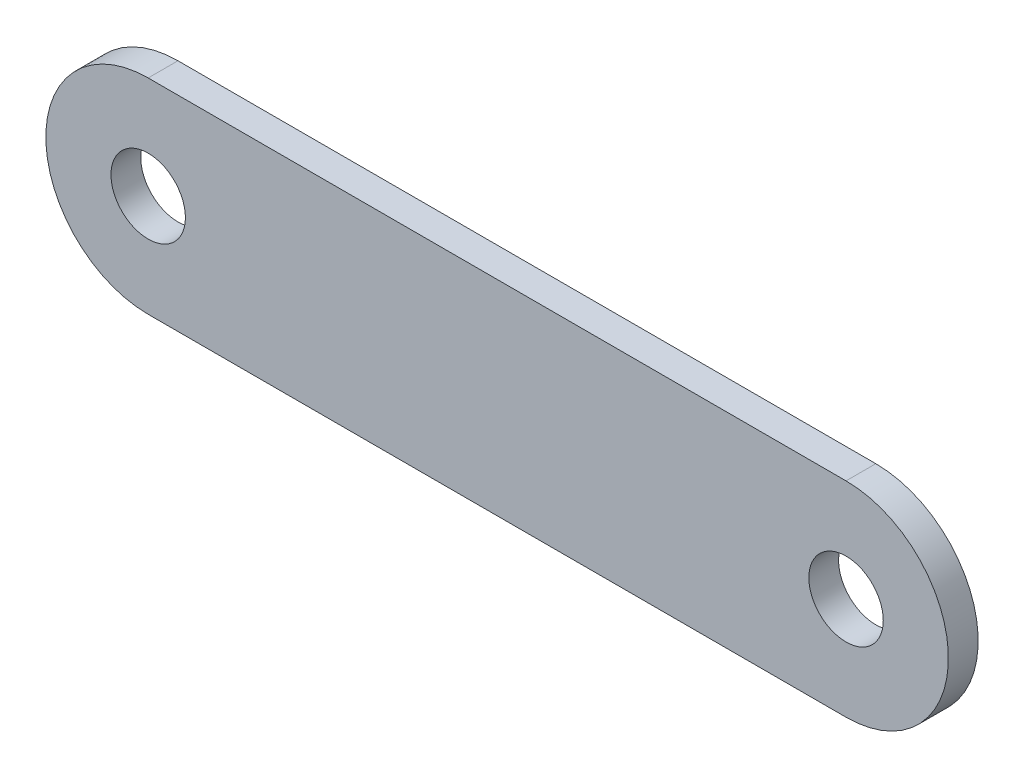
SolidWorks part; units mm, degrees
material "Plain Carbon Steel"
ref_plane "Front Plane" through (0, 0, 0) normal (0, 0, 1) x (1, 0, 0)
ref_plane "Top Plane" through (0, 0, 0) normal (0, 1, 0) x (1, 0, 0)
ref_plane "Right Plane" through (0, 0, 0) normal (1, 0, 0) x (0, 0, -1)
sketch "Sketch1" plane through (0, 0, 0) normal (0, 0, 1) x (1, 0, 0)
  line L0 (0, 11) -> (75, 11)
  line L1 (0, -11) -> (75, -11)
  circle A0 centre (0, 0) radius 4
  circle A1 centre (75, 0) radius 4
  arc A2 (0, 11) -> (0, -11) centre (0, 0) ccw
  arc A3 (75, 11) -> (75, -11) centre (75, 0) cw
  dimension "D1" = 8
  dimension "D2" = 8
  dimension "D3" = 75
  dimension "D4" = 22
  dimension "D5" = 11
extrude "Boss-Extrude1" add sketch "Sketch1" along normal blind 3.2
